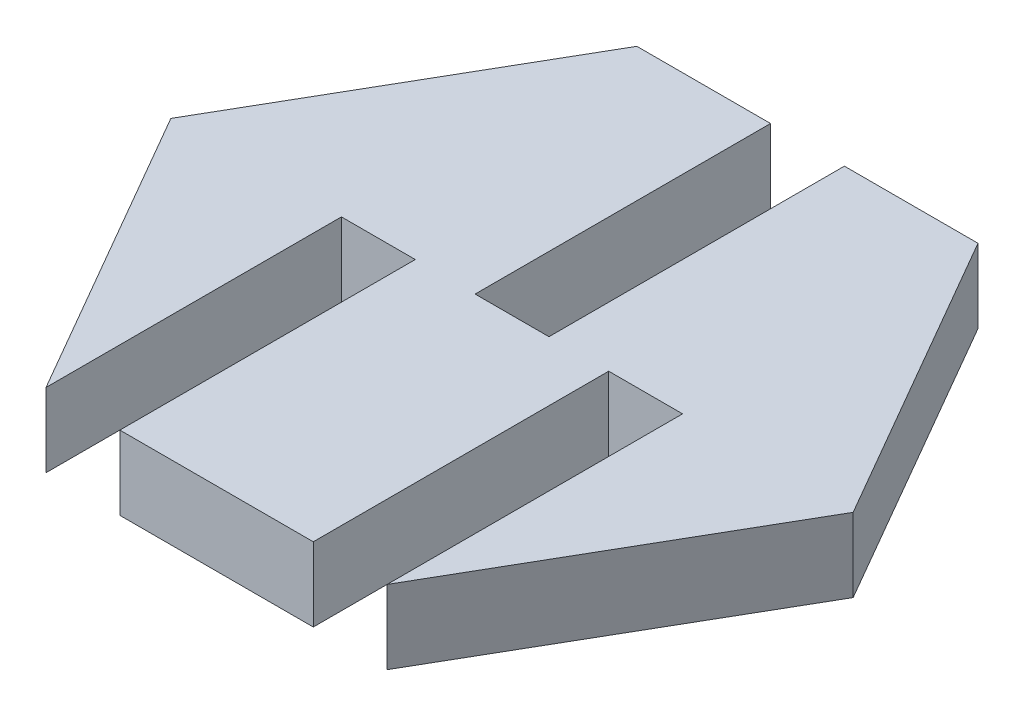
SolidWorks part; units mm, degrees
ref_plane "Front Plane" through (0, 0, 0) normal (0, 0, 1) x (1, 0, 0)
ref_plane "Top Plane" through (0, 0, 0) normal (0, 1, 0) x (1, 0, 0)
ref_plane "Right Plane" through (0, 0, 0) normal (1, 0, 0) x (0, 0, -1)
sketch "Sketch1" plane through (0, 0, 0) normal (0, 1, 0) x (1, 0, 0)
  line L1 (11.547, 0) -> (5.7735, 10)
  line L2 (5.7735, 10) -> (-5.7735, 10)
  line L3 (-5.7735, 10) -> (-11.547, 0)
  line L4 (-11.547, 0) -> (-5.7735, -10)
  line L5 (-5.7735, -10) -> (5.7735, -10)
  line L6 (5.7735, -10) -> (11.547, 0)
  circle A0 centre (0, 0) radius 10 construction
  dimension "D1" = 20
extrude "Boss-Extrude1" add sketch "Sketch1" along normal blind 2.5
sketch "Sketch5" plane through (0, 0, 10) normal (0, 0, 1) x (1, 0, 0)
  line L0 (-5.7735, 0) -> (5.7735, 0) construction
  line L1 (-5.7735, 2.5) -> (-3.2735, 2.5)
  line L2 (-5.7735, 2.5) -> (-5.7735, 0)
  line L3 (-5.7735, 0) -> (-3.2735, 0)
  line L4 (-3.2735, 2.5) -> (-3.2735, 0)
  dimension "D1" = 2.5
extrude "Cut-Extrude3" cut sketch "Sketch5" against normal blind 10
sketch "Sketch6" plane through (0, 0, 10) normal (0, 0, 1) x (1, 0, 0)
  line L0 (-3.2735, 0) -> (5.7735, 0) construction
  line L1 (5.7735, 2.5) -> (3.2735, 2.5)
  line L2 (5.7735, 2.5) -> (5.7735, 0)
  line L3 (5.7735, 0) -> (3.2735, 0)
  line L4 (3.2735, 2.5) -> (3.2735, 0)
  dimension "D1" = 2.5
extrude "Cut-Extrude4" cut sketch "Sketch6" against normal blind 10
sketch "Sketch7" plane through (0, 0, -10) normal (0, 0, -1) x (-1, 0, 0)
  line L0 (-5.7735, 2.5) -> (5.7735, 2.5) construction
  line L1 (1.2485, 2.5) -> (-1.2515, 2.5)
  line L2 (1.2485, 2.5) -> (1.2485, 0)
  line L3 (1.2485, 0) -> (-1.2515, 0)
  line L4 (-1.2515, 2.5) -> (-1.2515, 0)
  line L5 (-5.7735, 0) -> (5.7735, 0) construction
  line L6 (5.7735, 2.5) -> (5.7735, 0) construction
  dimension "D1" = 2.5
  dimension "D2" = 4.525
extrude "Cut-Extrude5" cut sketch "Sketch7" against normal blind 10
